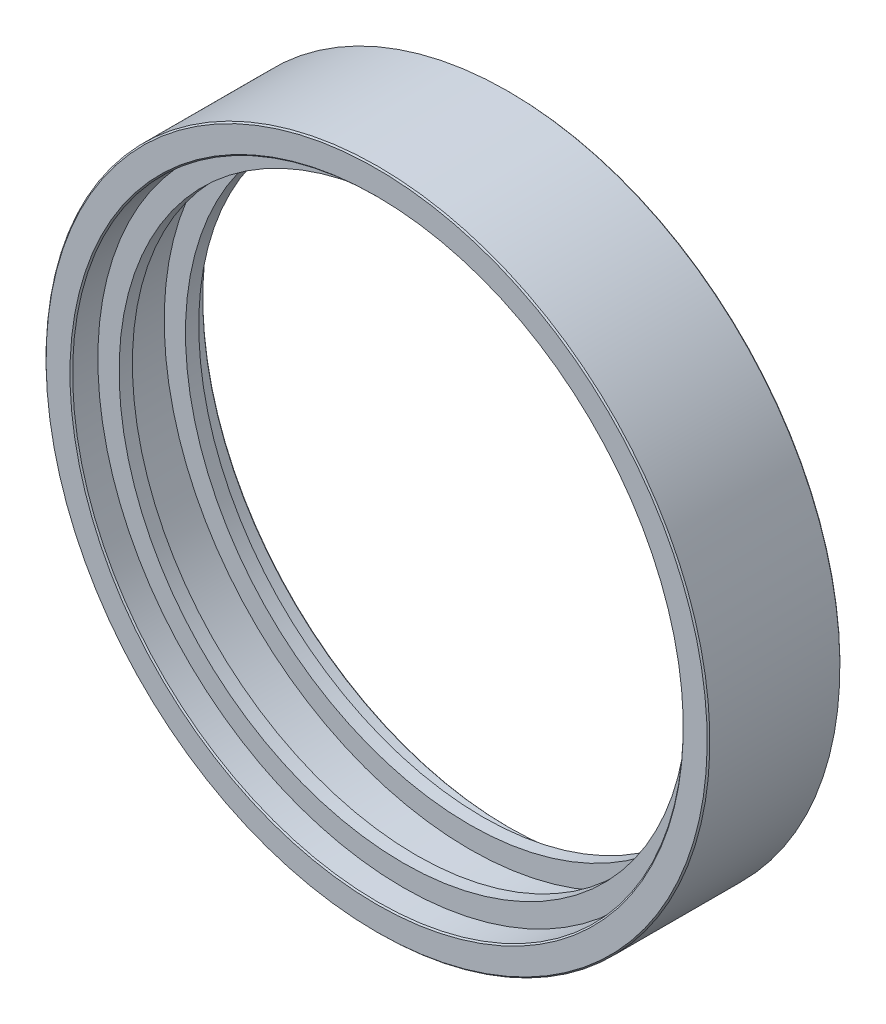
SolidWorks part; units mm, degrees
ref_plane "Piano frontale" through (0, 0, 0) normal (0, 0, 1) x (1, 0, 0)
ref_plane "Piano superiore" through (0, 0, 0) normal (0, 1, 0) x (1, 0, 0)
ref_plane "Piano destro" through (0, 0, 0) normal (1, 0, 0) x (0, 0, -1)
sketch "Schizzo2" plane through (0, 0, 0) normal (1, 0, 0) x (0, 0, -1)
  line L0 (0.5634, 12.5) -> (5.5634, 12.5)
  line L1 (5.5634, 12.5) -> (5.5634, 11.5)
  line L2 (5.5634, 11.5) -> (4.5634, 11.5)
  line L3 (4.5634, 11.5) -> (4.5634, 10.7)
  line L4 (4.5634, 10.7) -> (4.0634, 10.7)
  line L5 (4.0634, 10.7) -> (4.0634, 11.5)
  line L6 (4.0634, 11.5) -> (2.0634, 11.5)
  line L7 (2.0634, 11.5) -> (2.0634, 10.7)
  line L8 (2.0634, 10.7) -> (1.5634, 10.7)
  line L9 (1.5634, 10.7) -> (1.5634, 11.5)
  line L10 (1.5634, 11.5) -> (0.5634, 11.5)
  line L11 (0.5634, 11.5) -> (0.5634, 12.5)
  line L12 (0, 0) -> (-8.7302, 0) construction
  dimension "D1" = 5
  dimension "D2" = 1
  dimension "D3" = 1
  dimension "D4" = 0.8
  dimension "D5" = 1
  dimension "D6" = 0.5
  dimension "D7" = 0.5
  dimension "D8" = 12.5
revolve "Rivoluzione1" add sketch "Schizzo2" angle 360 about L12
chamfer "Smusso1" distance 0.05 angle 45 4 edges at (0, 11.5, -5.5634) (0, 12.5, -5.5634) (0, 12.5, -0.5634) (0, 11.5, -0.5634)
